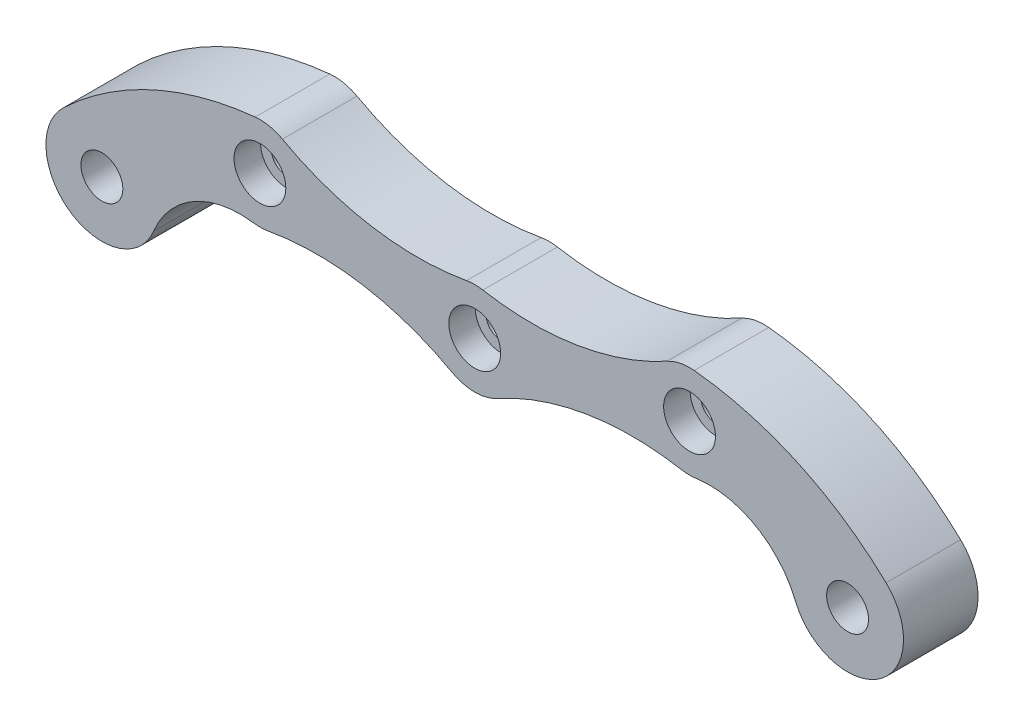
SolidWorks part; units mm, degrees
ref_plane "Front Plane" through (0, 0, 0) normal (0, 0, 1) x (1, 0, 0)
ref_plane "Top Plane" through (0, 0, 0) normal (0, 1, 0) x (1, 0, 0)
ref_plane "Right Plane" through (0, 0, 0) normal (1, 0, 0) x (0, 0, -1)
sketch "Sketch1" plane through (0, 0, 0) normal (0, 0, 1) x (1, 0, 0)
  line L0 (0, 0) -> (0, 3.81) construction
  line L5 (0, 3.81) -> (-23.045, 3.81) construction
  line L6 (0, 3.81) -> (23.045, 3.81) construction
  line L7 (-40, -5) -> (40, -5) construction
  line L8 (0, 0) -> (0, -5) construction
  arc A0 (-44.1294, -0.6471) -> (-34.4435, -7.2638) centre (-40, -5) ccw
  arc A1 (34.4435, -7.2638) -> (44.1294, -0.6471) centre (40, -5) ccw
  arc A2 (-2.4149, -4.3782) -> (2.4149, -4.3782) centre (0, 0) ccw
  arc A3 (-23.7575, -1.139) -> (-22.1678, -1.1124) centre (-23.045, 3.81) ccw
  arc A4 (22.1678, -1.1124) -> (23.7575, -1.139) centre (23.045, 3.81) ccw
  arc A5 (-44.1294, -0.6471) -> (-23.5456, 8.7849) centre (-20.0413, -26.0393) cw
  arc A6 (-0.8772, 4.9224) -> (-20.6301, 8.1882) centre (-6.1407, 34.4571) cw
  arc A7 (-34.4435, -7.2638) -> (-23.7575, -1.139) centre (-25.1826, -11.0369) cw
  arc A8 (-22.1678, -1.1124) -> (-2.4149, -4.3782) centre (-16.9043, -30.6471) cw
  arc A9 (0.8772, 4.9224) -> (20.6301, 8.1882) centre (6.1407, 34.4571) ccw
  arc A10 (22.1678, -1.1124) -> (2.4149, -4.3782) centre (16.9043, -30.6471) ccw
  arc A11 (34.4435, -7.2638) -> (23.7575, -1.139) centre (25.1826, -11.0369) ccw
  arc A12 (44.1294, -0.6471) -> (23.5456, 8.7849) centre (20.0413, -26.0393) ccw
  arc A13 (-34, -5) -> (-44.1294, -0.6471) centre (-40, -5) ccw construction
  arc A14 (-23.5456, 8.7849) -> (-23.7575, -1.139) centre (-23.045, 3.81) ccw construction
  arc A15 (-20.6301, 8.1882) -> (-23.5456, 8.7849) centre (-23.045, 3.81) ccw
  arc A16 (-22.1678, -1.1124) -> (-18.045, 3.81) centre (-23.045, 3.81) ccw construction
  arc A17 (-18.045, 3.81) -> (-20.6301, 8.1882) centre (-23.045, 3.81) ccw construction
  arc A18 (-0.8772, 4.9224) -> (-2.4149, -4.3782) centre (0, 0) ccw construction
  arc A19 (0.8772, 4.9224) -> (-0.8772, 4.9224) centre (0, 0) ccw
  arc A20 (2.4149, -4.3782) -> (0.8772, 4.9224) centre (0, 0) ccw construction
  arc A21 (18.045, 3.81) -> (22.1678, -1.1124) centre (23.045, 3.81) ccw construction
  arc A22 (23.5456, 8.7849) -> (20.6301, 8.1882) centre (23.045, 3.81) ccw
  arc A23 (23.7575, -1.139) -> (23.5456, 8.7849) centre (23.045, 3.81) ccw construction
  arc A24 (20.6301, 8.1882) -> (18.045, 3.81) centre (23.045, 3.81) ccw construction
  arc A25 (44.1294, -0.6471) -> (34, -5) centre (40, -5) ccw construction
  arc A26 (34, -5) -> (34.4435, -7.2638) centre (40, -5) ccw construction
  arc A27 (-34.4435, -7.2638) -> (-34, -5) centre (-40, -5) ccw construction
  point P4 (23.045, 3.81)
  point P5 (-23.045, 3.81)
  point P6 (-40, -5)
  point P8 (40, -5)
  point P9 (0, 0)
  dimension "D5" = 10
  dimension "D6" = 12
  dimension "D7" = 35
  dimension "D8" = 30
  dimension "D9" = 30
  dimension "D10" = 10
  dimension "D1" = 46.09
  dimension "D2" = 3.81
  dimension "D3" = 80
  dimension "D4" = 5
extrude "Boss-Extrude1" add sketch "Sketch1" along normal mid plane 8
sketch "Sketch2" plane through (0, 0, 4) normal (0, 0, 1) x (1, 0, 0)
  point P0 (-23.045, 3.81)
  point P1 (0, 0)
  point P3 (23.045, 3.81)
hole_wizard "CBORE for #4 Socket Head Cap Screw1" positions "Sketch2" profile "Sketch3" counterbore size "#4" standard "ANSI Inch"
sketch "Sketch3" plane through (-23.045, 3.81, 4) normal (1, 0, 0) x (0, -1, 0)
  line L0 (0, 0) -> (0, 10)
  line L1 (0, 10) -> (1.6319, 9.0194)
  line L2 (1.6319, 9.0194) -> (1.6319, 2.8448)
  line L3 (1.6319, 2.8448) -> (2.7788, 2.8448)
  line L4 (2.7788, 2.8448) -> (2.7788, 0)
  line L5 (2.7788, 0) -> (0, 0)
  line L10 (0, 10) -> (-1.632, 9.0194) construction
  line L11 (0, -6.35) -> (0, 107.95) construction
  dimension "Hole Dia." = 3.2639
  dimension "Hole Depth" = 10
  dimension "C'Bore Dia." = 5.5575
  dimension "C'Bore Depth" = 2.8448
  dimension "Drill Angle" = 118
sketch "Sketch5" plane through (0, 0, -4) normal (0, 0, -1) x (-1, 0, 0)
  point P0 (-40, -5)
  point P1 (40, -5)
hole_wizard "CBORE for #8 Socket Head Cap Screw1" positions "Sketch5" profile "Sketch6" counterbore size "#8" standard "ANSI Inch"
sketch "Sketch6" plane through (40, -5, -4) normal (1, 0, 0) x (0, 1, 0)
  line L0 (0, 0) -> (0, 10)
  line L1 (0, 10) -> (2.2479, 8.6493)
  line L2 (2.2479, 8.6493) -> (2.2479, 4.1656)
  line L3 (2.2479, 4.1656) -> (3.9688, 4.1656)
  line L4 (3.9688, 4.1656) -> (3.9688, 0)
  line L5 (3.9688, 0) -> (0, 0)
  line L10 (0, 10) -> (-2.2479, 8.6493) construction
  line L11 (0, -6.35) -> (0, 107.95) construction
  dimension "Hole Dia." = 4.4958
  dimension "Hole Depth" = 10
  dimension "C'Bore Dia." = 7.9375
  dimension "C'Bore Depth" = 4.1656
  dimension "Drill Angle" = 118
